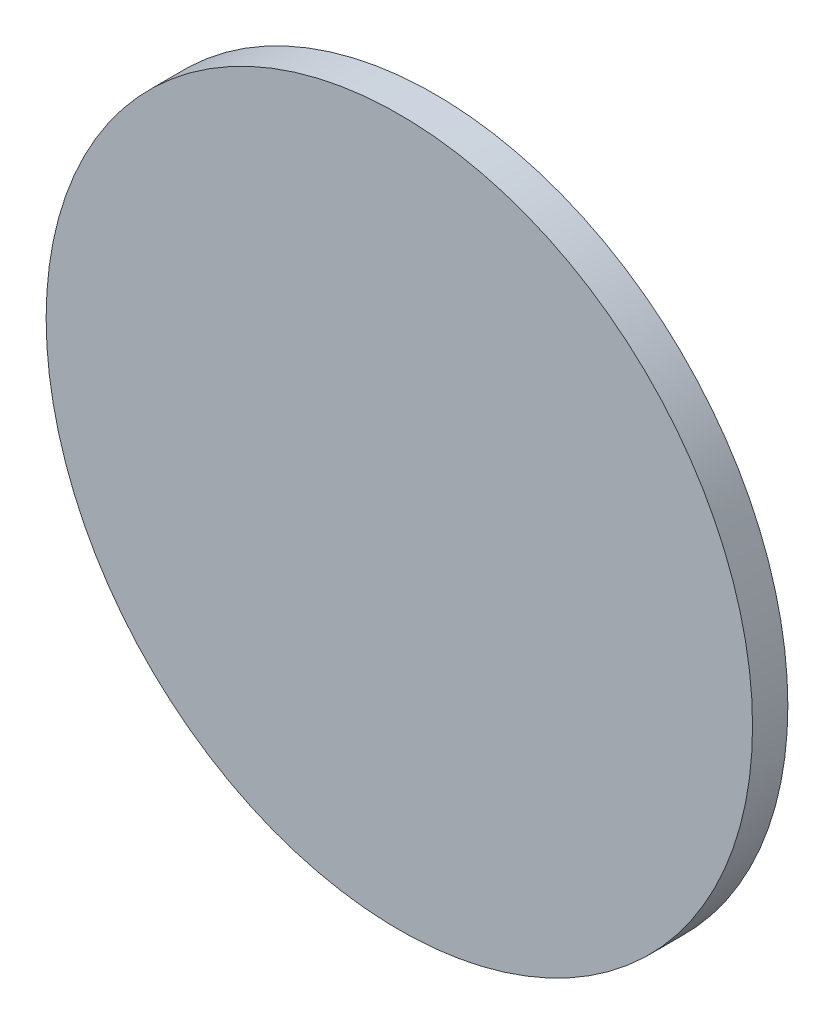
SolidWorks part; units mm, degrees
ref_plane "前视基准面" through (0, 0, 0) normal (0, 0, 1) x (1, 0, 0)
ref_plane "上视基准面" through (0, 0, 0) normal (0, 1, 0) x (1, 0, 0)
ref_plane "右视基准面" through (0, 0, 0) normal (1, 0, 0) x (0, 0, -1)
sketch "草图1" plane through (0, 0, 0) normal (0, 0, 1) x (1, 0, 0)
  circle A0 centre (0, 0) radius 20
  dimension "D1" = 40
extrude "凸台-拉伸1" add sketch "草图1" along normal blind 2 contours A0
